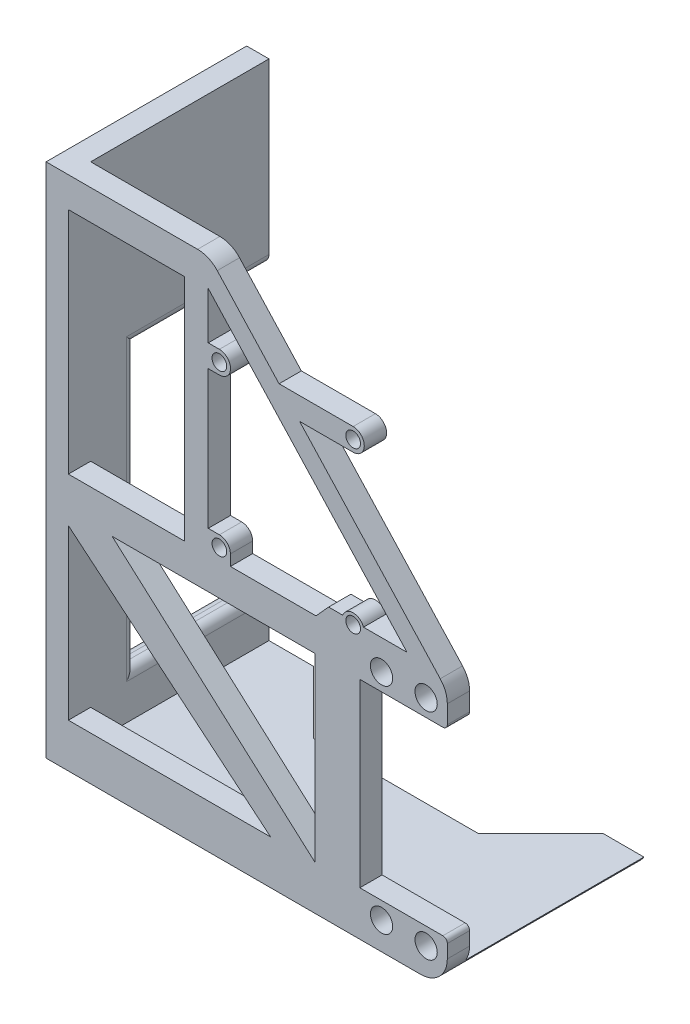
SolidWorks part; units mm, degrees
ref_plane "前视基准面" through (0, 0, 0) normal (0, 0, 1) x (1, 0, 0)
ref_plane "上视基准面" through (0, 0, 0) normal (0, 1, 0) x (1, 0, 0)
ref_plane "右视基准面" through (0, 0, 0) normal (1, 0, 0) x (0, 0, -1)
sketch "草图2" plane through (0, 0, 0) normal (0, 0, 1) x (1, 0, 0)
  line L0 (90, -0.0335) -> (90, 7.1636)
  line L2 (0, 0) -> (0, 113)
  line L3 (0, 113) -> (36.6134, 113)
  line L5 (90, 7.1636) -> (70.3734, 7.1636)
  line L6 (70.3734, 7.1636) -> (70.3734, 47.6636)
  line L7 (70.3734, 47.6636) -> (90, 47.6636)
  line L8 (90, 47.6636) -> (90, 55.0711)
  line L10 (36.6134, 113) -> (52.2619, 96.0201)
  line L11 (90, 47.6636) -> (90, 7.1636) construction
  line L12 (80.9641, 58.203) -> (71.1966, 58.203)
  line L13 (36.373, 106.588) -> (80.9641, 58.203)
  line L14 (14.8145, 47.6636) -> (60.373, 47.6636)
  line L15 (31, 106.2259) -> (5, 106.2259)
  line L16 (36.373, 59.9897) -> (36.373, 91.0201)
  line L17 (31, 106.2259) -> (31, 54.841)
  line L21 (60.373, 47.6636) -> (60.373, 7.0335)
  line L22 (31, 54.841) -> (11.373, 54.841)
  line L23 (5, 54.841) -> (5, 91.0201)
  line L25 (5, 44.841) -> (5, 7.0335)
  line L26 (41.373, 55.0711) -> (60.537, 55.0711)
  line L28 (50.373, 7.0335) -> (5, 7.0335)
  line L29 (5, 44.841) -> (50.373, 7.0335)
  line L30 (14.8145, 47.6636) -> (60.373, 7.0335)
  line L31 (0, 0) -> (0, -2.8364)
  line L32 (0, -2.8364) -> (90, -2.8364)
  line L33 (90, -0.0335) -> (90, -2.8364)
  line L34 (60.537, 55.0711) -> (63.373, 58.203)
  line L36 (85.2437, 51.5186) -> (75.2437, 51.5186) construction
  line L37 (5, 7.0335) -> (10, 7.0335)
  line L38 (70.3734, 27.4136) -> (128.7612, 27.4136) construction
  line L39 (38.873, 57.5201) -> (68.873, 57.5201) construction
  line L42 (36.373, 59.9897) -> (38.873, 59.9897)
  line L45 (85.2437, 51.5186) -> (85.2437, 3.3086) construction
  line L46 (38.873, 57.5201) -> (38.873, 93.5201) construction
  line L49 (38.873, 96.0201) -> (36.373, 96.0201)
  line L51 (38.873, 91.0201) -> (36.373, 91.0201)
  line L53 (40.6408, 95.2878) -> (36.373, 91.0201) construction
  line L54 (40.6408, 91.7523) -> (36.373, 96.0201) construction
  line L56 (66.5495, 58.203) -> (63.373, 58.203)
  line L57 (70.3751, 58.203) -> (67.371, 58.203)
  line L58 (52.2619, 96.0201) -> (68.873, 96.0201)
  line L59 (6.373, 54.841) -> (5, 54.841)
  line L60 (36.373, 96.0201) -> (36.373, 106.588)
  line L61 (38.873, 93.5201) -> (68.873, 93.5201) construction
  line L62 (68.873, 91.0201) -> (56.8698, 91.0201)
  line L63 (56.8698, 91.0201) -> (90, 55.0711)
  line L65 (5, 96.0201) -> (5, 106.2259)
  line L67 (41.3427, 57.5201) -> (41.3427, 55.0711)
  line L68 (41.3427, 55.0711) -> (41.373, 55.0711)
  line L69 (5, 96.0201) -> (5, 91.0201)
  line L70 (6.373, 54.841) -> (11.373, 54.841)
  circle A0 centre (85.2437, 51.5186) radius 2.5
  circle A1 centre (75.2437, 51.5186) radius 2.5
  circle A2 centre (75.2437, 3.3086) radius 2.5
  circle A3 centre (85.2437, 3.3086) radius 2.5
  arc A4 (38.873, 59.9897) -> (41.3427, 57.5201) centre (38.873, 57.5201) cw
  circle A5 centre (38.873, 57.5201) radius 1.65
  circle A6 centre (38.873, 93.5201) radius 1.65
  arc A7 (38.873, 91.0201) -> (38.873, 96.0201) centre (38.873, 93.5201) ccw
  circle A10 centre (68.873, 57.5201) radius 1.65
  arc A12 (66.5495, 58.203) -> (71.1966, 58.203) centre (68.873, 57.3648) cw
  circle A13 centre (68.873, 93.5201) radius 1.65
  arc A14 (68.873, 96.0201) -> (68.873, 91.0201) centre (68.873, 93.5201) cw
  point P8 (5, 7.0335)
  point P35 (85.2437, 51.5186)
  point P48 (38.873, 59.5799)
extrude "凸台-拉伸1" add sketch "草图2" along normal blind 5
sketch "草图3" plane through (0, 0, 0) normal (0, 0, -1) x (-1, 0, 0)
  line L1 (0, 0) -> (-90, 0)
  line L2 (0, 0) -> (0, -2.8364)
  line L3 (0, -2.8364) -> (-90, -2.8364)
  line L4 (-90, 0) -> (-90, -2.8364)
  line L5 (0, 113) -> (-5, 113)
  line L6 (0, 113) -> (0, 7.0335)
  line L7 (0, 7.0335) -> (-5, 7.0335)
  line L8 (-5, 113) -> (-5, 7.0335)
  line L9 (-5, 7.0335) -> (0, 7.0335)
  line L10 (-5, 7.0335) -> (-5, 0)
  line L11 (-5, 0) -> (0, 0)
  line L12 (0, 7.0335) -> (0, 0)
  line M13 (-90, 7.1636) -> (-90, -2.8364)
  line M14 (-90, -2.8364) -> (0, -2.8364)
  line M15 (0, -2.8364) -> (0, 113)
  line M16 (0, 113) -> (-36.6134, 113)
  line M28 (-5, 106.2259) -> (-5, 54.841)
  line M29 (-5, 44.841) -> (-5, 7.0335)
extrude "凸台-拉伸2" add sketch "草图3" along normal blind 40 contours L1 M15 M13 M14 | L7 L10 L1 M15 | L8 L7 M16 M28 M29 M15
sketch "草图6" plane through (5, 0, 0) normal (1, 0, 0) x (0, 0, -1)
  line L0 (40, 113) -> (40, 73) construction
  line L1 (40, 113) -> (40, 0) construction
  line L2 (40, 0) -> (40, 10) construction
  line L3 (0, 7.0335) -> (10, 7.0335) construction
  line L5 (40, 10) -> (10, 10)
  line L6 (40, 10) -> (40, 73)
  line L7 (40, 73) -> (10, 73)
  line L8 (10, 10) -> (10, 73)
extrude "切除-拉伸1" cut sketch "草图6" against normal up to next
sketch "草图7" plane through (0, 0, 0) normal (0, 1, 0) x (1, 0, 0)
  line L1 (5, 40) -> (90, 40) construction
  line L5 (80, 40) -> (66, 26)
  line L7 (15, 40) -> (29, 26)
  line L8 (29, 26) -> (66, 26)
  line L9 (15, 40) -> (80, 40)
  point P0 (0, 0)
extrude "切除-拉伸2" cut sketch "草图7" against normal blind 10
fillet "圆角1" radius 6 3 edges at (90, -2.8364, -17.5) (90, 55.0711, 2.5) (36.6134, 113, 2.5)
fillet "圆角2" radius 2 6 edges at (5, 41.5, -10) (0, 41.5, -10) (0, 73, -25) (5, 73, -25) (0, 10, -25) (5, 10, -25)
fillet "圆角3" radius 1 2 edges at (90, 7.1636, 2.5) (90, 47.6636, 2.5)
